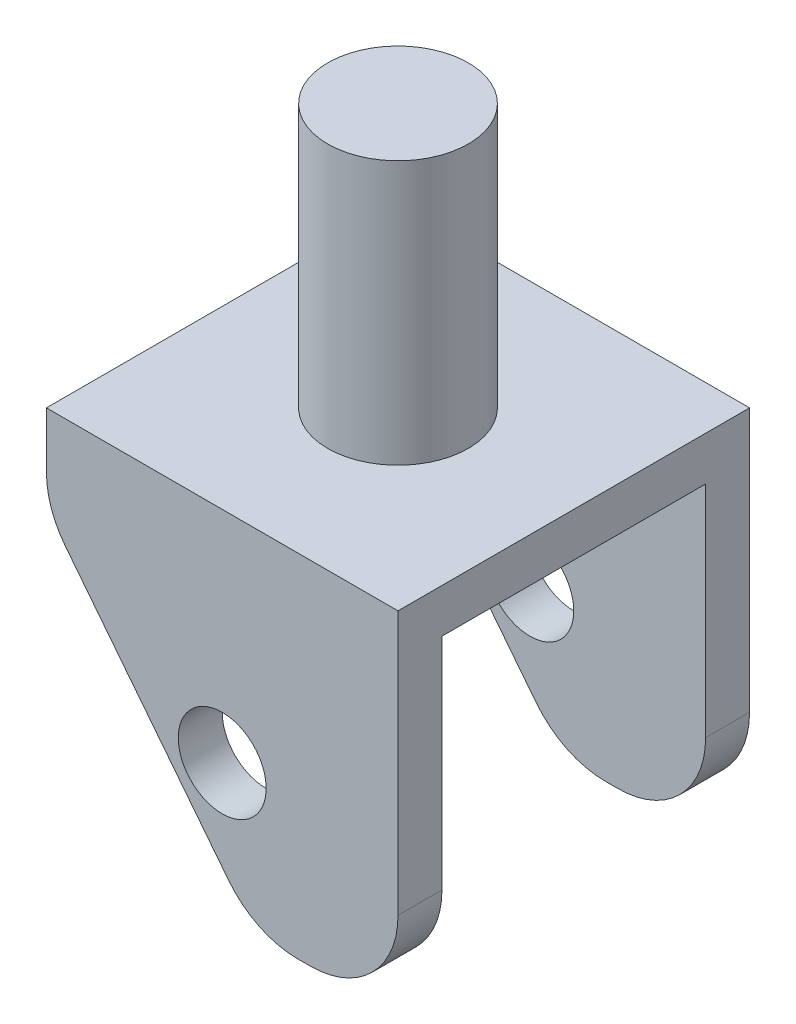
SolidWorks part; units mm, degrees
ref_plane "Płaszczyzna przednia" through (0, 0, 0) normal (0, 0, 1) x (1, 0, 0)
ref_plane "Płaszczyzna górna" through (0, 0, 0) normal (0, 1, 0) x (1, 0, 0)
ref_plane "Płaszczyzna prawa" through (0, 0, 0) normal (1, 0, 0) x (0, 0, -1)
sketch "Szkic1" plane through (0, 0, 0) normal (0, 0, 1) x (1, 0, 0)
  line L1 (-8.9902, 22.9172) -> (31.0098, 22.9172)
  line L2 (-8.9902, 22.9172) -> (-8.9902, 13.1059)
  line L3 (14.7326, -17.0828) -> (31.0098, -17.0828)
  line L4 (31.0098, 22.9172) -> (31.0098, -17.0828)
  line L5 (-8.9902, 13.1059) -> (14.7326, -17.0828)
  dimension "D1" = 40
  dimension "D2" = 40
extrude "Dodanie-wyciągnięcie1" add sketch "Szkic1" along normal blind 40 contours L1 L4 L3 L5 L2
sketch "Szkic2" plane through (31.0098, 0, 0) normal (1, 0, 0) x (0, 0, -1)
  line L0 (-40, -17.0828) -> (0, -17.0828) construction
  line L1 (-35, -17.0828) -> (-5, -17.0828)
  line L2 (-35, -17.0828) -> (-35, 17.9172)
  line L3 (-35, 17.9172) -> (-5, 17.9172)
  line L4 (-5, -17.0828) -> (-5, 17.9172)
  line L5 (-40, 22.9172) -> (0, 22.9172) construction
  line L6 (-40, 22.9172) -> (-40, -17.0828) construction
  line L7 (0, 22.9172) -> (0, -17.0828) construction
  dimension "D1" = 5
  dimension "D2" = 5
  dimension "D3" = 5
extrude "Wytnij-wyciągnięcie1" cut sketch "Szkic2" against normal blind 40
sketch "Szkic3" plane through (0, 0, 0) normal (0, 0, -1) x (-1, 0, 0)
  line L0 (-11.0098, 22.9172) -> (-11.0098, -17.2972) construction
  line L1 (8.9902, 22.9172) -> (-31.0098, 22.9172) construction
  line L2 (-14.7326, -17.0828) -> (-31.0098, -17.0828) construction
  circle A0 centre (-11.0098, -2.0828) radius 5
  dimension "D1" = 15
extrude "Wytnij-wyciągnięcie2" cut sketch "Szkic3" against normal blind 40
fillet "Zaokrąglenie1" radius 10 6 edges at (31.0098, -17.0828, 37.5) (31.0098, -17.0828, 2.5) (-8.9902, 13.1059, 37.5) (-8.9902, 13.1059, 2.5) (14.7326, -17.0828, 37.5) (14.7326, -17.0828, 2.5)
sketch "Szkic4" plane through (0, 22.9172, 0) normal (0, 1, 0) x (1, 0, 0)
  line L0 (-8.9902, 0) -> (31.0098, -40) construction
  line L1 (31.0098, 0) -> (-8.9902, -40) construction
  circle A0 centre (11.0098, -20) radius 8
extrude "Dodanie-wyciągnięcie2" add sketch "Szkic4" along normal blind 30
